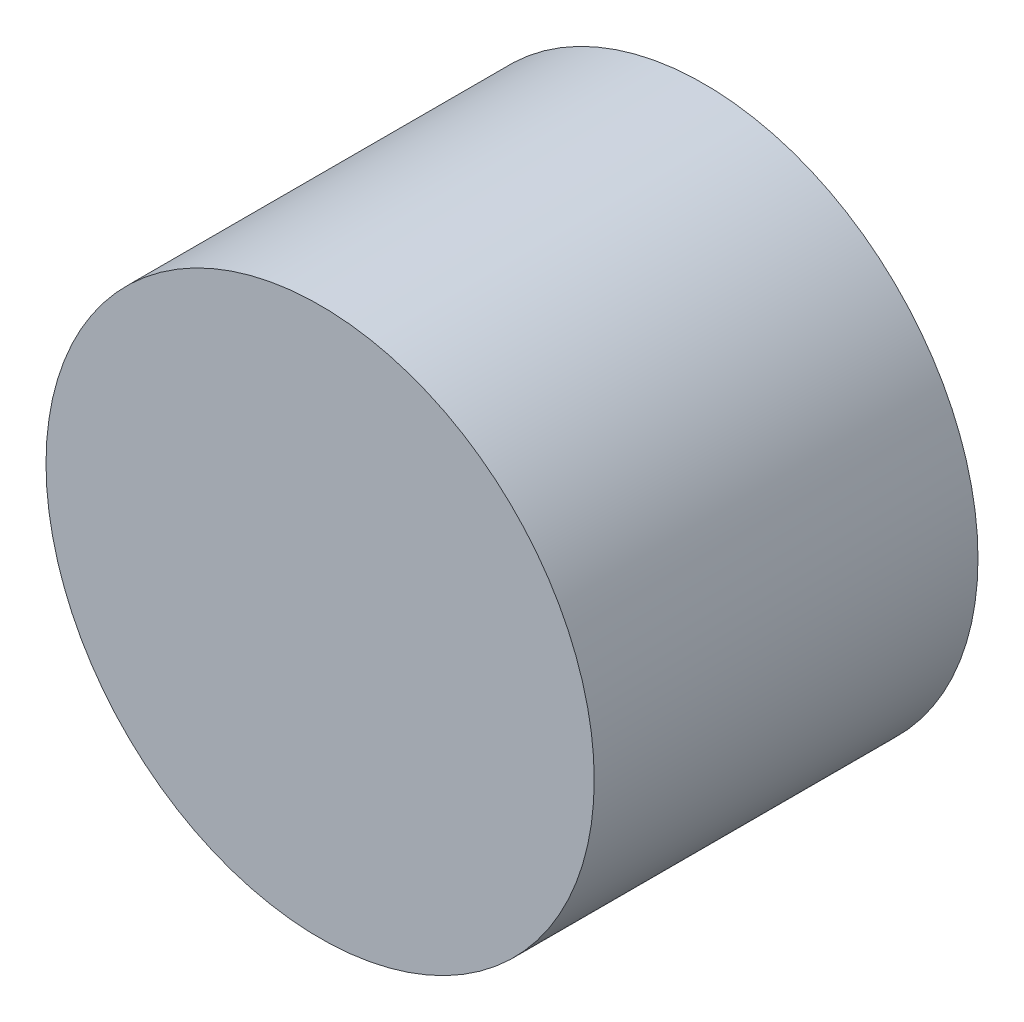
SolidWorks part; units mm, degrees
ref_plane "Front Plane" through (0, 0, 0) normal (0, 0, 1) x (1, 0, 0)
ref_plane "Top Plane" through (0, 0, 0) normal (0, 1, 0) x (1, 0, 0)
ref_plane "Right Plane" through (0, 0, 0) normal (1, 0, 0) x (0, 0, -1)
sketch "Sketch1" plane through (0, 0, 0) normal (0, 1, 0) x (1, 0, 0)
  line L0 (-1.55, 0) -> (-1.55, 2)
  line L1 (0, 0) -> (-5, 0)
  line L2 (0, 0) -> (0, -7)
  line L3 (0, -7) -> (-5, -7)
  line L4 (-5, 0) -> (-5, -7)
  line L5 (-1.55, 0) -> (0, 0)
  line L6 (-1.55, 0) -> (-1.55, -5)
  line L7 (-1.55, -5) -> (0, -5)
  line L8 (0, 0) -> (0, -5)
  line L9 (-1.55, 2) -> (-5, 0)
  dimension "D1" = 5
  dimension "D2" = 7
  dimension "D3" = 5
  dimension "D4" = 1.55
  dimension "D5" = 2
revolve "Revolve2" add sketch "Sketch1" angle 360 about L2
